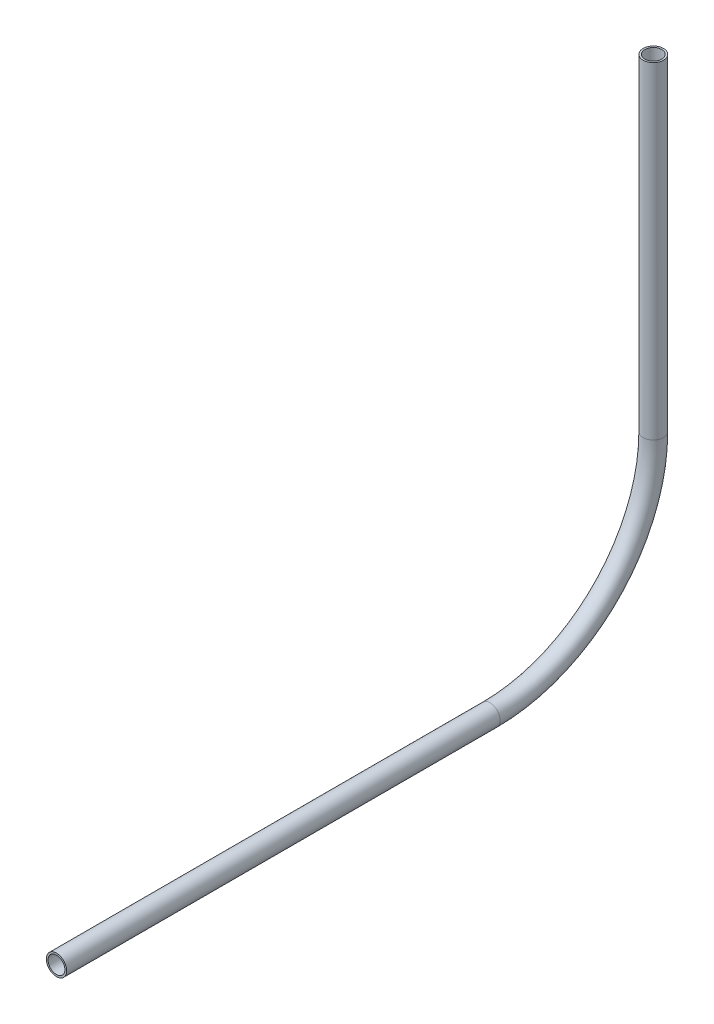
SolidWorks part; units mm, degrees
ref_plane "Front Plane" through (0, 0, 0) normal (0, 0, 1) x (1, 0, 0)
ref_plane "Top Plane" through (0, 0, 0) normal (0, 1, 0) x (1, 0, 0)
ref_plane "Right Plane" through (0, 0, 0) normal (1, 0, 0) x (0, 0, -1)
sketch "Sketch1" plane through (0, 0, 0) normal (1, 0, 0) x (0, 0, -1)
  line L0 (-303.1646, 599.96) -> (-168.2735, 599.96)
  line L1 (-117.4735, 650.76) -> (-117.4735, 752.4586)
  arc A0 (-168.2735, 599.96) -> (-117.4735, 650.76) centre (-168.2735, 650.76) ccw
  dimension "D1" = 50.8
other "Pipe 0.5 SCH 40(1)"
ref_plane "Plane1" through (0, 599.96, 303.1646) normal (0, 0, -1) x (0, 1, 0)
sketch "Sketch11" plane through (0, 599.96, 303.1646) normal (0, 0, -1) x (0, 1, 0)
  circle A0 centre (0, 0) radius 3.175
  circle A1 centre (0, 0) radius 2.6162
  point P5 (0, 0)
  dimension "In_dia" = 6.35
  dimension "Out_dia" = 5.2324
